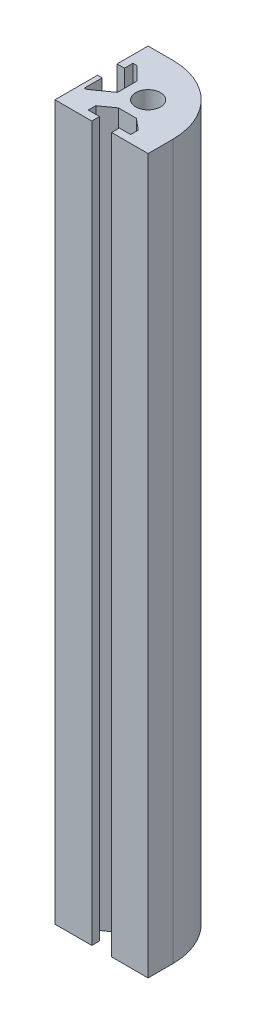
SolidWorks part; units mm, degrees
ref_plane "Front" through (0, 0, 0) normal (0, 0, 1) x (1, 0, 0)
ref_plane "Top" through (0, 0, 0) normal (0, 1, 0) x (1, 0, 0)
ref_plane "Right" through (0, 0, 0) normal (1, 0, 0) x (0, 0, -1)
sketch "Croquis1" plane through (0, 0, 0) normal (0, 1, 0) x (1, 0, 0)
  line L0 (-7, 15) -> (-15, 15)
  line L1 (-15, 15) -> (15, 15) construction
  line L2 (-15, 15) -> (-15, -15) construction
  line L3 (-15, -15) -> (15, -15) construction
  line L4 (15, 15) -> (15, -15) construction
  line L5 (-15, 15) -> (15, -15) construction
  line L6 (-15, -15) -> (15, 15) construction
  line L7 (-15, 15) -> (-15, 5.0276)
  line L8 (-15, 5.0276) -> (-12.6234, 5.0276)
  line L9 (-12.6234, 5.0276) -> (-12.6234, 7.7527)
  line L10 (-12.6234, 7.7527) -> (-11.3205, 7.7527)
  line L11 (-11.3205, 7.7527) -> (-7, 3.4321)
  line L12 (-7, 3.4321) -> (-7, -2.8611)
  line L13 (-7, -2.8611) -> (-12.793, -7)
  line L14 (-12.793, -7) -> (-13.5273, -7)
  line L15 (-13.5273, -7) -> (-13.5273, -1.258)
  line L16 (-13.5273, -1.258) -> (-15, -1.258)
  line L17 (-15, -1.258) -> (-15, -15)
  line L18 (-15, -15) -> (-3.1399, -15)
  line L19 (-3.1399, -15) -> (-3.1399, -12.5058)
  line L20 (-3.1399, -12.5058) -> (-6.779, -12.5058)
  line L21 (-6.779, -12.5058) -> (-6.779, -10.0798)
  line L22 (-6.779, -10.0798) -> (-2.5129, -7.0319)
  line L23 (-2.5129, -7.0319) -> (3.2559, -7.0319)
  line L24 (3.2559, -7.0319) -> (6.8949, -10.0798)
  line L25 (6.8949, -10.0798) -> (6.8949, -12.5058)
  line L26 (6.8949, -12.5058) -> (3.2559, -12.5058)
  line L27 (3.2559, -12.5058) -> (3.2559, -15)
  line L28 (3.2559, -15) -> (15, -15)
  line L29 (15, -15) -> (15, -7)
  line L30 (0, 0) -> (-50000, 0) construction
  line L31 (0, 0) -> (0, -50000) construction
  circle A0 centre (0, 0) radius 4
  arc A1 (-7, 15) -> (15, -7) centre (-7, -7) cw
  point P0 (0, 0)
  dimension "D3" = 8
  dimension "D4" = 22
  dimension "D1" = 30
  dimension "D2" = 30
extrude "Saliente-Extruir1" add sketch "Croquis1" along normal blind 230
